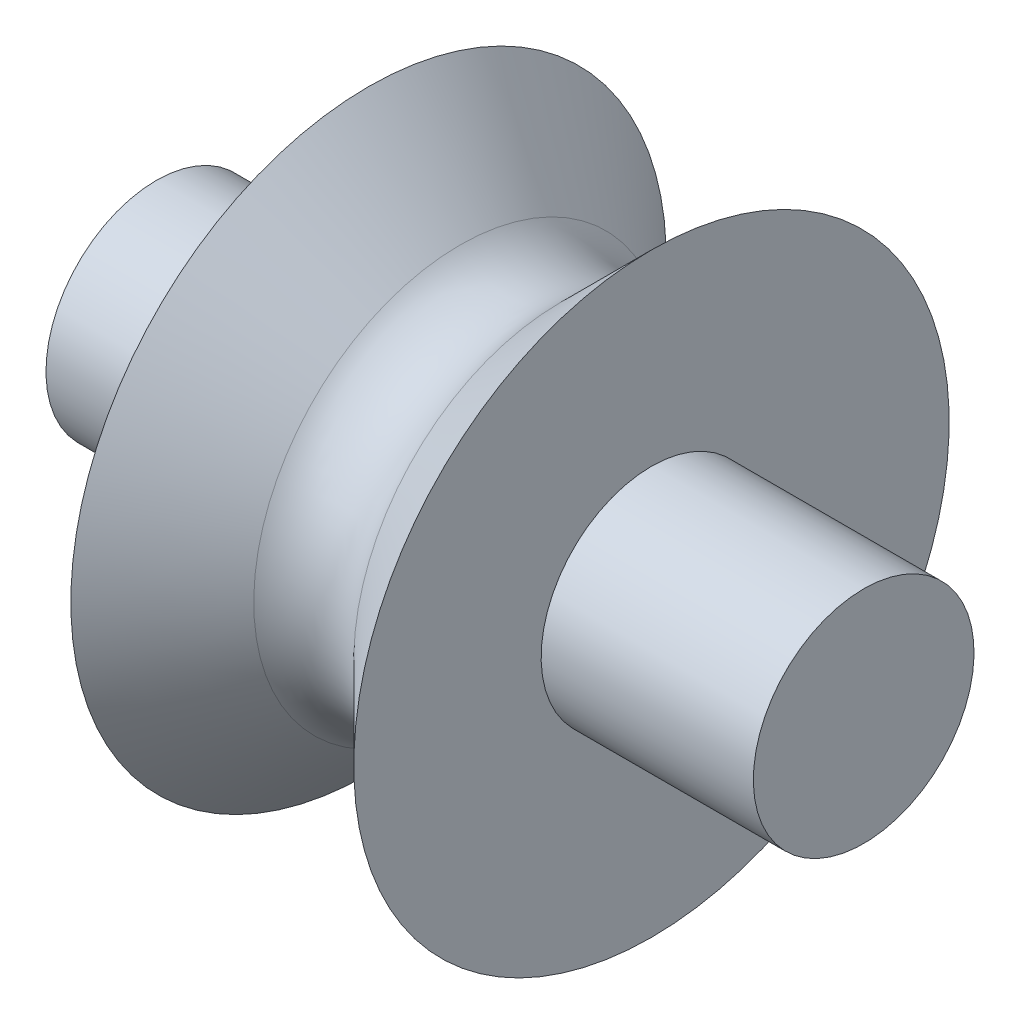
SolidWorks part; units mm, degrees
ref_plane "Front Plane" through (0, 0, 0) normal (0, 0, 1) x (1, 0, 0)
ref_plane "Top Plane" through (0, 0, 0) normal (0, 1, 0) x (1, 0, 0)
ref_plane "Right Plane" through (0, 0, 0) normal (1, 0, 0) x (0, 0, -1)
sketch "Sketch1" plane through (0, 0, 0) normal (0, 0, 1) x (1, 0, 0)
  line L0 (0, 0) -> (7.62, 0)
  line L1 (7.62, 0) -> (7.62, 6.7269)
  line L2 (7.62, 6.7269) -> (10.9039, 3.4429)
  line L3 (14.4961, 3.4429) -> (17.78, 6.7269)
  line L4 (17.78, 6.7269) -> (17.78, 0)
  line L5 (17.78, 0) -> (25.4, 0)
  line L6 (25.4, 0) -> (25.4, -3.9624)
  line L7 (25.4, -3.9624) -> (0, -3.9624)
  line L8 (0, -3.9624) -> (0, 0)
  arc A1 (14.4961, 3.4429) -> (10.9039, 3.4429) centre (12.7, 5.239) cw
  point P5 (17.887, 13.1524)
  point P11 (12.8633, 5.7365)
  point P12 (8.7965, 13.1524)
  point P13 (12.026, 7.7699)
  point P14 (12.026, 8.4876)
  point P17 (17.78, 6.7012)
  point P18 (17.78, 7.6042)
  dimension "D1" = 2.54
  dimension "D2" = 3.9624
  dimension "D3" = 25.4
  dimension "D4" = 7.62
revolve "Revolve1" add sketch "Sketch1" angle 360 about L7
